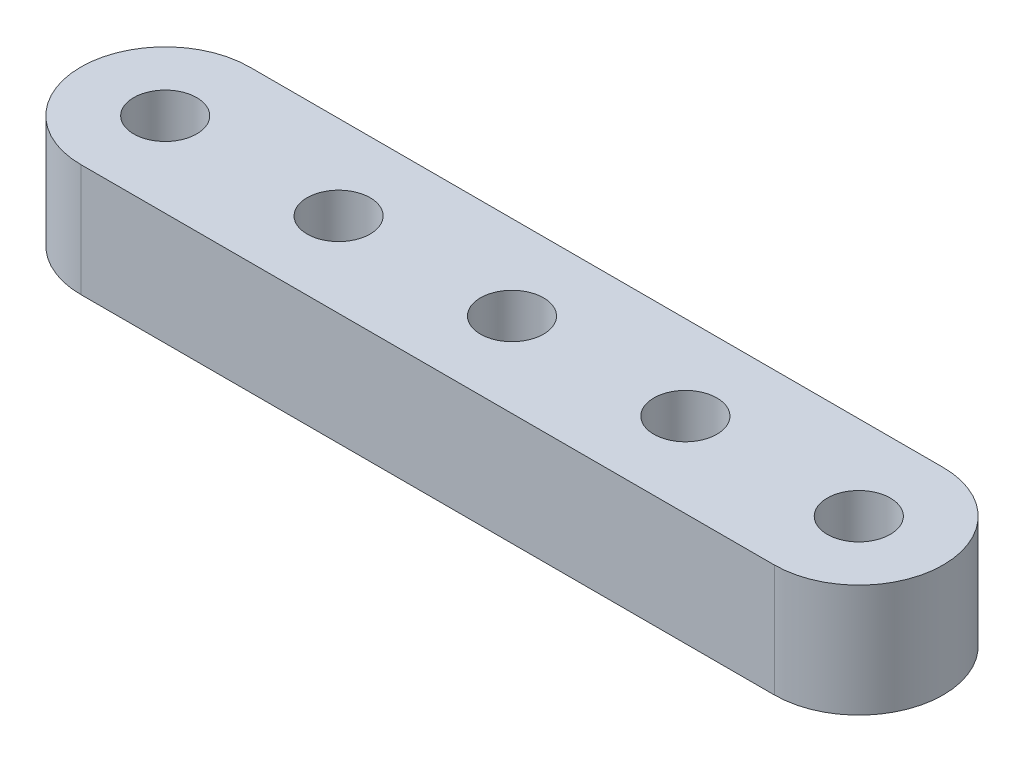
SolidWorks part; units mm, degrees
ref_plane "Front Plane" through (0, 0, 0) normal (0, 0, 1) x (1, 0, 0)
ref_plane "Top Plane" through (0, 0, 0) normal (0, 1, 0) x (1, 0, 0)
ref_plane "Right Plane" through (0, 0, 0) normal (1, 0, 0) x (0, 0, -1)
ref_plane "Plane1" through (0, 6.35, 0) normal (0, 1, 0) x (1, 0, 0)
sketch "Sketch1" plane through (0, 6.35, 0) normal (0, 1, 0) x (1, 0, 0)
  line L0 (19.558, 4.7625) -> (-19.558, 4.7625)
  line L1 (-19.558, -4.7625) -> (19.558, -4.7625)
  arc A0 (19.558, -4.7625) -> (19.558, 4.7625) centre (19.558, 0) ccw
  arc A1 (-19.558, 4.7625) -> (-19.558, -4.7625) centre (-19.558, 0) ccw
  circle A2 centre (19.558, 0) radius 1.778
  circle A3 centre (9.779, 0) radius 1.778
  circle A4 centre (0, 0) radius 1.778
  circle A5 centre (-9.779, 0) radius 1.778
  circle A6 centre (-19.558, 0) radius 1.778
extrude "Boss-Extrude1" add sketch "Sketch1" against normal blind 6.35
